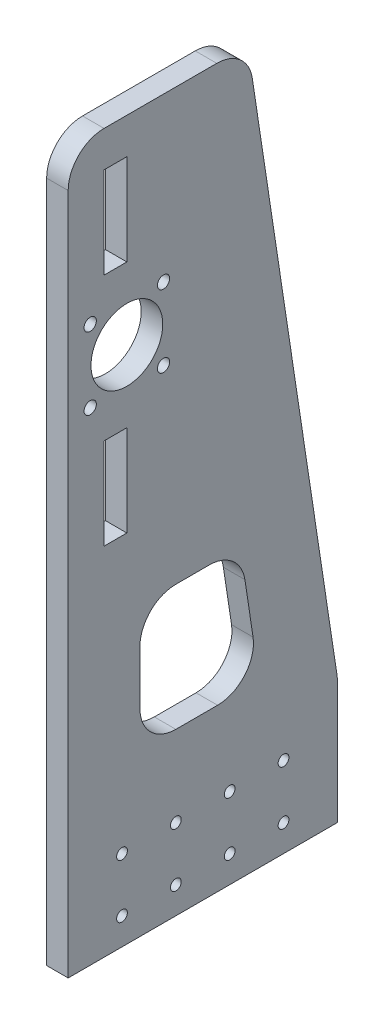
SolidWorks part; units mm, degrees
ref_plane "Alzado" through (0, 0, 0) normal (0, 0, 1) x (1, 0, 0)
ref_plane "Planta" through (0, 0, 0) normal (0, 1, 0) x (1, 0, 0)
ref_plane "Vista lateral" through (0, 0, 0) normal (1, 0, 0) x (0, 0, -1)
sketch "Croquis1" plane through (0, 0, 0) normal (1, 0, 0) x (0, 0, -1)
  line L0 (0, 0) -> (0, 380)
  line L1 (20, 400) -> (82.802, 400)
  line L2 (32.7, 329.2) -> (32.7, 289.2) construction
  line L3 (150, 0) -> (0, 0)
  line L4 (30, 45) -> (30, 15) construction
  line L5 (30, 15) -> (60, 15) construction
  line L6 (60, 15) -> (60, 45) construction
  line L7 (60, 45) -> (90, 45) construction
  line L8 (90, 45) -> (90, 15) construction
  line L9 (90, 15) -> (120, 15) construction
  line L10 (120, 15) -> (120, 45) construction
  line L11 (150, 0) -> (150, 68.4934)
  line L12 (149.7743, 71.4896) -> (102.5763, 382.9961)
  line L13 (20, 380) -> (32.7, 380)
  line L14 (20, 380) -> (20, 329.2)
  line L15 (20, 329.2) -> (32.7, 329.2)
  line L16 (32.7, 380) -> (32.7, 329.2)
  line L17 (20, 249.2) -> (32.7, 249.2)
  line L18 (20, 249.2) -> (20, 198.4)
  line L19 (20, 198.4) -> (32.7, 198.4)
  line L20 (32.7, 249.2) -> (32.7, 198.4)
  line L21 (32.7, 289.2) -> (32.7, 249.2) construction
  line L22 (12.2738, 309.3201) -> (12.2738, 269.0799) construction
  line L23 (12.2738, 269.0799) -> (53.1262, 269.0799) construction
  line L24 (53.1262, 269.0799) -> (53.1262, 309.3201) construction
  line L25 (53.1262, 309.3201) -> (32.7, 289.2) construction
  line L26 (32.7, 289.2) -> (12.2738, 269.0799) construction
  line L27 (60, 90) -> (83.2546, 90)
  line L28 (103.0289, 112.9961) -> (98.4835, 142.9961)
  line L29 (78.7091, 160) -> (60, 160)
  line L30 (40, 140) -> (40, 110)
  circle A0 centre (30, 45) radius 3
  circle A1 centre (60, 45) radius 3
  circle A2 centre (90, 45) radius 3
  circle A3 centre (120, 45) radius 3
  circle A4 centre (30, 15) radius 3
  circle A5 centre (60, 15) radius 3
  circle A6 centre (90, 15) radius 3
  circle A7 centre (120, 15) radius 3
  arc A8 (150, 68.4934) -> (149.7743, 71.4896) centre (130, 68.4934) ccw
  arc A9 (0, 380) -> (20, 400) centre (20, 380) cw
  arc A10 (82.802, 400) -> (102.5763, 382.9961) centre (82.802, 380) cw
  circle A11 centre (32.7, 289.2) radius 20
  circle A12 centre (12.2738, 309.3201) radius 3.4252
  circle A13 centre (53.1262, 309.3201) radius 3.4252
  circle A14 centre (53.1262, 269.0799) radius 3.4252
  circle A15 centre (12.2738, 269.0799) radius 3.4252
  arc A16 (83.2546, 90) -> (103.0289, 112.9961) centre (83.2546, 110) ccw
  arc A17 (60, 90) -> (40, 110) centre (60, 110) cw
  arc A18 (60, 160) -> (40, 140) centre (60, 140) ccw
  arc A19 (98.4835, 142.9961) -> (78.7091, 160) centre (78.7091, 140) ccw
  point P24 (150, 70)
  point P27 (0, 400)
  point P30 (100, 400)
  dimension "D1" = 30
  dimension "D8" = 20
  dimension "D10" = 6
  dimension "D16" = 40
  dimension "D17" = 40
  dimension "D21" = 20
  dimension "D2" = 30
  dimension "D3" = 150
  dimension "D4" = 400
  dimension "D5" = 100
  dimension "D6" = 30
  dimension "D7" = 70
  dimension "D9" = 30
  dimension "D11" = 50.8
  dimension "D12" = 12.7
  dimension "D13" = 20
  dimension "D14" = 20
  dimension "D15" = 80
  dimension "D18" = 40
  dimension "D19" = 90
  dimension "D20" = 70
extrude "Saliente-Extruir1" add sketch "Croquis1" along normal blind 12 contours A10 L1 A9 L0 L3 L11 A8 L12 A15 A14 A13 A12 A11 A7 A6 A5 A4 A3 A2 A1 A0 L13 L16 L15 L14 L17 L20 L19 L18
